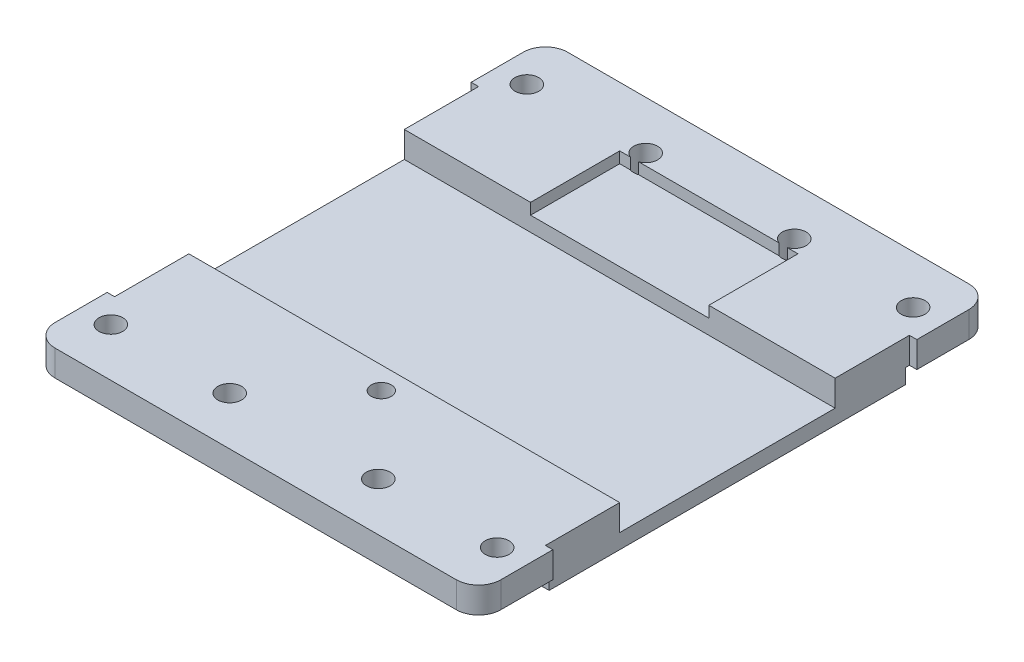
SolidWorks part; units mm, degrees
ref_plane "Front Plane" through (0, 0, 0) normal (0, 0, 1) x (1, 0, 0)
ref_plane "Top Plane" through (0, 0, 0) normal (0, 1, 0) x (1, 0, 0)
ref_plane "Right Plane" through (0, 0, 0) normal (1, 0, 0) x (0, 0, -1)
sketch "Sketch1" plane through (0, 0, 0) normal (0, 1, 0) x (1, 0, 0)
  line L0 (23.0945, -31.0966) -> (27.0945, -31.0966)
  line L1 (30.0945, -28.0966) -> (30.0945, -20.5966)
  line L2 (30.0945, -20.5966) -> (-29.9055, -20.5966)
  line L3 (-29.9055, -20.5966) -> (-29.9055, -28.0966)
  line L4 (-26.9055, -31.0966) -> (-24.9055, -31.0966)
  line L5 (-24.9055, -31.0966) -> (-24.9055, -29.0966)
  line L6 (-24.9055, -29.0966) -> (-14.9055, -29.0966)
  line L7 (-14.9055, -29.0966) -> (-14.9055, -31.0966)
  line L8 (-14.9055, -31.0966) -> (13.0945, -31.0966)
  line L9 (13.0945, -31.0966) -> (13.0945, -29.0966)
  line L10 (13.0945, -29.0966) -> (23.0945, -29.0966)
  line L11 (23.0945, -29.0966) -> (23.0945, -31.0966)
  line L12 (-22.9055, 37.9034) -> (-26.9055, 37.9034)
  line L13 (-29.9055, 34.9034) -> (-29.9055, 27.4034)
  line L14 (-29.9055, 27.4034) -> (30.0945, 27.4034)
  line L15 (30.0945, 27.4034) -> (30.0945, 34.9034)
  line L16 (27.0945, 37.9034) -> (25.0945, 37.9034)
  line L17 (25.0945, 37.9034) -> (25.0945, 35.9034)
  line L18 (25.0945, 35.9034) -> (15.0945, 35.9034)
  line L19 (15.0945, 35.9034) -> (15.0945, 37.9034)
  line L20 (15.0945, 37.9034) -> (-12.9055, 37.9034)
  line L21 (-12.9055, 37.9034) -> (-12.9055, 35.9034)
  line L22 (-12.9055, 35.9034) -> (-22.9055, 35.9034)
  line L23 (-22.9055, 35.9034) -> (-22.9055, 37.9034)
  line L24 (30.0945, 27.4034) -> (30.0945, -20.5966)
  line L25 (-29.9055, 27.4034) -> (-29.9055, -20.5966)
  arc A0 (27.0945, -31.0966) -> (30.0945, -28.0966) centre (27.0945, -28.0966) ccw
  arc A1 (-29.9055, -28.0966) -> (-26.9055, -31.0966) centre (-26.9055, -28.0966) ccw
  arc A2 (-26.9055, 37.9034) -> (-29.9055, 34.9034) centre (-26.9055, 34.9034) ccw
  arc A3 (30.0945, 34.9034) -> (27.0945, 37.9034) centre (27.0945, 34.9034) ccw
extrude "Boss-Extrude1" add sketch "Sketch1" along normal blind 2 contours L14 L25 L2 L24 | L3 A1 L4 L5 L6 L7 L8 L9 L10 L11 L0 A0 L1 L2 | L15 A3 L16 L17 L18 L19 L20 L21 L22 L23 L12 A2 L13 L14
sketch "Sketch2" plane through (0, 2, 0) normal (0, 1, 0) x (1, 0, 0)
  line L1 (-50.1539, 17.9034) -> (43.4526, 17.9034)
  line L2 (-50.1539, 17.9034) -> (-50.1539, -11.0966)
  line L3 (-50.1539, -11.0966) -> (43.4526, -11.0966)
  line L4 (43.4526, 17.9034) -> (43.4526, -11.0966)
  line L20 (30.0945, -28.0966) -> (30.0945, 34.9034)
  line L21 (27.0945, 37.9034) -> (25.0945, 37.9034)
  line L22 (25.0945, 37.9034) -> (25.0945, 35.9034)
  line L23 (25.0945, 35.9034) -> (15.0945, 35.9034)
  line L24 (15.0945, 35.9034) -> (15.0945, 37.9034)
  line L25 (15.0945, 37.9034) -> (-12.9055, 37.9034)
  line L26 (-12.9055, 37.9034) -> (-12.9055, 35.9034)
  line L27 (-12.9055, 35.9034) -> (-22.9055, 35.9034)
  line L28 (-22.9055, 35.9034) -> (-22.9055, 37.9034)
  line L29 (-22.9055, 37.9034) -> (-26.9055, 37.9034)
  line L30 (-29.9055, 34.9034) -> (-29.9055, -28.0966)
  line L31 (-26.9055, -31.0966) -> (-24.9055, -31.0966)
  line L32 (-24.9055, -31.0966) -> (-24.9055, -29.0966)
  line L33 (-24.9055, -29.0966) -> (-14.9055, -29.0966)
  line L34 (-14.9055, -29.0966) -> (-14.9055, -31.0966)
  line L35 (-14.9055, -31.0966) -> (13.0945, -31.0966)
  line L36 (13.0945, -31.0966) -> (13.0945, -29.0966)
  line L37 (13.0945, -29.0966) -> (23.0945, -29.0966)
  line L38 (23.0945, -29.0966) -> (23.0945, -31.0966)
  line L39 (23.0945, -31.0966) -> (27.0945, -31.0966)
  line L40 (30.0945, -28.0966) -> (30.0945, 34.9034)
  line L41 (27.0945, 37.9034) -> (25.0945, 37.9034)
  line L42 (25.0945, 37.9034) -> (25.0945, 35.9034)
  line L43 (25.0945, 35.9034) -> (15.0945, 35.9034)
  line L44 (15.0945, 35.9034) -> (15.0945, 37.9034)
  line L45 (15.0945, 37.9034) -> (-12.9055, 37.9034)
  line L46 (-12.9055, 37.9034) -> (-12.9055, 35.9034)
  line L47 (-12.9055, 35.9034) -> (-22.9055, 35.9034)
  line L48 (-22.9055, 35.9034) -> (-22.9055, 37.9034)
  line L49 (-22.9055, 37.9034) -> (-26.9055, 37.9034)
  line L50 (-29.9055, 34.9034) -> (-29.9055, -28.0966)
  line L51 (-26.9055, -31.0966) -> (-24.9055, -31.0966)
  line L52 (-24.9055, -31.0966) -> (-24.9055, -29.0966)
  line L53 (-24.9055, -29.0966) -> (-14.9055, -29.0966)
  line L54 (-14.9055, -29.0966) -> (-14.9055, -31.0966)
  line L55 (-14.9055, -31.0966) -> (13.0945, -31.0966)
  line L56 (13.0945, -31.0966) -> (13.0945, -29.0966)
  line L57 (13.0945, -29.0966) -> (23.0945, -29.0966)
  line L58 (23.0945, -29.0966) -> (23.0945, -31.0966)
  line L59 (23.0945, -31.0966) -> (27.0945, -31.0966)
  arc A4 (30.0945, 34.9034) -> (27.0945, 37.9034) centre (27.0945, 34.9034) ccw
  arc A5 (-26.9055, 37.9034) -> (-29.9055, 34.9034) centre (-26.9055, 34.9034) ccw
  arc A6 (-29.9055, -28.0966) -> (-26.9055, -31.0966) centre (-26.9055, -28.0966) ccw
  arc A7 (27.0945, -31.0966) -> (30.0945, -28.0966) centre (27.0945, -28.0966) ccw
  arc A8 (30.0945, 34.9034) -> (27.0945, 37.9034) centre (27.0945, 34.9034) ccw
  arc A9 (-26.9055, 37.9034) -> (-29.9055, 34.9034) centre (-26.9055, 34.9034) ccw
  arc A10 (-29.9055, -28.0966) -> (-26.9055, -31.0966) centre (-26.9055, -28.0966) ccw
  arc A11 (27.0945, -31.0966) -> (30.0945, -28.0966) centre (27.0945, -28.0966) ccw
  line M29 (30.0945, -28.0966) -> (30.0945, 34.9034)
  arc M30 (30.0945, 34.9034) -> (27.0945, 37.9034) centre (27.0945, 34.9034) ccw
  line M31 (27.0945, 37.9034) -> (25.0945, 37.9034)
  line M32 (25.0945, 37.9034) -> (25.0945, 35.9034)
  line M33 (25.0945, 35.9034) -> (15.0945, 35.9034)
  line M34 (15.0945, 35.9034) -> (15.0945, 37.9034)
  line M35 (15.0945, 37.9034) -> (-12.9055, 37.9034)
  line M36 (-12.9055, 37.9034) -> (-12.9055, 35.9034)
  line M37 (-12.9055, 35.9034) -> (-22.9055, 35.9034)
  line M38 (-22.9055, 35.9034) -> (-22.9055, 37.9034)
  line M39 (-22.9055, 37.9034) -> (-26.9055, 37.9034)
  arc M40 (-26.9055, 37.9034) -> (-29.9055, 34.9034) centre (-26.9055, 34.9034) ccw
  line M41 (-29.9055, 34.9034) -> (-29.9055, -28.0966)
  arc M42 (-29.9055, -28.0966) -> (-26.9055, -31.0966) centre (-26.9055, -28.0966) ccw
  line M43 (-26.9055, -31.0966) -> (-24.9055, -31.0966)
  line M44 (-24.9055, -31.0966) -> (-24.9055, -29.0966)
  line M45 (-24.9055, -29.0966) -> (-14.9055, -29.0966)
  line M46 (-14.9055, -29.0966) -> (-14.9055, -31.0966)
  line M47 (-14.9055, -31.0966) -> (13.0945, -31.0966)
  line M48 (13.0945, -31.0966) -> (13.0945, -29.0966)
  line M49 (13.0945, -29.0966) -> (23.0945, -29.0966)
  line M50 (23.0945, -29.0966) -> (23.0945, -31.0966)
  line M51 (23.0945, -31.0966) -> (27.0945, -31.0966)
  arc M52 (27.0945, -31.0966) -> (30.0945, -28.0966) centre (27.0945, -28.0966) ccw
  dimension "D2" = 20
  dimension "D3" = 20
  dimension "D1" = 0
extrude "Boss-Extrude2" add sketch "Sketch2" along normal blind 3.5 contours L3 M41 M42 M43 M44 M45 M46 M47 M48 M49 M50 M51 M52 M29 | L1 M41 M29 M30 M31 M32 M33 M34 M35 M36 M37 M38 M39 M40
sketch "Sketch3" plane through (0, 5.5, 0) normal (0, 1, 0) x (1, 0, 0)
  line L0 (-29.9055, 17.9034) -> (-29.9055, -11.0966) construction
  line L1 (-35.4293, 27.9034) -> (-28.9055, 27.9034)
  line L2 (-35.4293, 27.9034) -> (-35.4293, -21.0966)
  line L3 (-35.4293, -21.0966) -> (-28.9055, -21.0966)
  line L4 (-28.9055, 27.9034) -> (-28.9055, -21.0966)
  line L5 (-14.9055, -31.0966) -> (13.0945, -31.0966) construction
  line L6 (15.0945, 37.9034) -> (-12.9055, 37.9034) construction
  line L7 (0.0945, 47.5005) -> (0.0945, -43.4412)
  line L8 (30.0945, 17.9034) -> (30.0945, -11.0966) construction
  line L9 (35.6184, -21.0966) -> (29.0945, -21.0966)
  line L10 (29.0945, 27.9034) -> (29.0945, -21.0966)
  line L11 (35.6184, 27.9034) -> (29.0945, 27.9034)
  line L12 (35.6184, 27.9034) -> (35.6184, -21.0966)
  dimension "D1" = 1
  dimension "D2" = 10
  dimension "D3" = 10
  dimension "D4" = 30
extrude "Cut-Extrude2" cut sketch "Sketch3" against normal blind 15 contours L12 L9 L10 L11 | L2 L3 L4 L1
sketch "Sketch4" plane through (0, 5.5, 0) normal (0, 1, 0) x (1, 0, 0)
  line L0 (-28.9055, 17.9034) -> (29.0945, 17.9034) construction
  line L1 (12.0945, 17.9034) -> (-11.9055, 17.9034)
  line L2 (12.0945, 17.9034) -> (12.0945, 29.9034)
  line L3 (12.0945, 29.9034) -> (-11.9055, 29.9034)
  line L4 (-11.9055, 17.9034) -> (-11.9055, 29.9034)
  line L5 (-28.9055, 27.9034) -> (-28.9055, 17.9034) construction
  dimension "D1" = 24
  dimension "D2" = 17
  dimension "D3" = 12
extrude "Cut-Extrude3" cut sketch "Sketch4" against normal blind 1.5
sketch "Sketch5" plane through (0, 5.5, 0) normal (0, 1, 0) x (1, 0, 0)
  line L0 (-28.9055, -11.0966) -> (29.0945, -11.0966) construction
  circle A0 centre (0, -14.0966) radius 1.35
  dimension "D1" = 2.7
  dimension "D2" = 3
extrude "Cut-Extrude4" cut sketch "Sketch5" against normal blind 3
sketch "Sketch6" plane through (0, 5.5, 0) normal (0, 1, 0) x (1, 0, 0)
  line L0 (-28.9055, -11.0966) -> (29.0945, -11.0966) construction
  line L1 (-28.9055, -11.0966) -> (29.0945, -11.0966) construction
  line L2 (52.5689, 3.4034) -> (-47.2679, 3.4034)
  line L3 (26.0945, 40.4034) -> (-25.9055, 40.4034) construction
  circle A0 centre (-20.188, -19.0966) radius 1.35
  circle A1 centre (0, -25.0966) radius 1.35
  circle A2 centre (20.7703, -19.0966) radius 1.35
  circle A3 centre (-20.188, 25.9034) radius 1.35
  circle A4 centre (0, 31.9034) radius 1.35
  circle A5 centre (20.7703, 25.9034) radius 1.35
  dimension "D1" = 8
  dimension "D2" = 14
  dimension "D3" = 8
  dimension "D4" = 2.7
  dimension "D5" = 2.7
  dimension "D6" = 2.7
  dimension "D7" = 37
extrude "Cut-Extrude5" cut sketch "Sketch6" against normal blind 3 contours A5 | A4 | A3 | A0 | A1 | A2
sketch "Sketch7" plane through (0, 0, 0) normal (0, -1, 0) x (1, 0, 0)
  line L0 (15.0945, -37.9034) -> (-12.9055, -37.9034) construction
  line L1 (-33.8076, 32.9113) -> (36.1224, 32.9113)
  line L2 (-33.8076, 32.9113) -> (-33.8076, 20.5966)
  line L3 (-33.8076, 20.5966) -> (36.1224, 20.5966)
  line L4 (36.1224, 32.9113) -> (36.1224, 20.5966)
  line L5 (-36.6663, -27.4034) -> (40.7404, -27.4034)
  line L6 (-36.6663, -27.4034) -> (-36.6663, -43.6031)
  line L7 (-36.6663, -43.6031) -> (40.7404, -43.6031)
  line L8 (40.7404, -27.4034) -> (40.7404, -43.6031)
  line L9 (-14.9055, 31.0966) -> (13.0945, 31.0966) construction
  dimension "D1" = 10.5
  dimension "D2" = 10.5
extrude "Cut-Extrude6" cut sketch "Sketch7" against normal blind 2
sketch "Sketch8" plane through (0, 2, 0) normal (0, -1, 0) x (1, 0, 0)
  line L0 (13.0945, 31.0966) -> (-14.9055, 31.0966) construction
  line L1 (30.0945, 28.0966) -> (30.0945, 21.0966) construction
  line L2 (-56.3939, -3.4034) -> (64.5651, -3.4034)
  line L3 (-12.9055, -37.9034) -> (15.0945, -37.9034) construction
  line L4 (0.0945, 49.059) -> (0.0945, -54.2227)
  circle A2 centre (10.0945, 24.5966) radius 1.6
  circle A3 centre (26.0945, 24.5966) radius 1.6
  circle A4 centre (-25.9055, 24.5966) radius 1.6
  circle A5 centre (-9.9055, 24.5966) radius 1.6
  circle A6 centre (26.0945, -31.4034) radius 1.6
  circle A7 centre (10.0945, -31.4034) radius 1.6
  circle A8 centre (-9.9055, -31.4034) radius 1.6
  circle A9 centre (-25.9055, -31.4034) radius 1.6
  dimension "D1" = 6.5
  dimension "D2" = 3.2
  dimension "D4" = 4
  dimension "D5" = 3.2
  dimension "D6" = 20
  dimension "D3" = 6.5
  dimension "D7" = 34.5
  dimension "D8" = 30
extrude "Cut-Extrude7" cut sketch "Sketch8" against normal blind 18 contours A9 | A8 | A7 | A6 | A3 | A2 | A5 | A4
sketch "Sketch9" plane through (0, 5.5, 0) normal (0, 1, 0) x (1, 0, 0)
  line L0 (12.0945, 29.9034) -> (10.6513, 29.9034) construction
  line L1 (-3.7538, -21.8858) -> (2.8434, -21.8858)
  line L2 (-3.7538, -21.8858) -> (-3.7538, -28.1897)
  line L3 (-3.7538, -28.1897) -> (2.8434, -28.1897)
  line L4 (2.8434, -21.8858) -> (2.8434, -28.1897)
  line L5 (17.4304, -16.3881) -> (23.3679, -16.3881)
  line L6 (17.4304, -16.3881) -> (17.4304, -21.8858)
  line L7 (17.4304, -21.8858) -> (23.3679, -21.8858)
  line L8 (23.3679, -16.3881) -> (23.3679, -21.8858)
  line L9 (-25.1579, -16.3881) -> (-17.388, -16.3881)
  line L10 (-25.1579, -16.3881) -> (-25.1579, -21.8858)
  line L11 (-25.1579, -21.8858) -> (-17.388, -21.8858)
  line L12 (-17.388, -16.3881) -> (-17.388, -21.8858)
  line L13 (-23.3254, 28.8391) -> (-18.1943, 28.8391)
  line L14 (-23.3254, 28.8391) -> (-23.3254, 23.6347)
  line L15 (-23.3254, 23.6347) -> (-18.1943, 23.6347)
  line L16 (-18.1943, 28.8391) -> (-18.1943, 23.6347)
  line L17 (-2.6543, 34.9965) -> (2.8434, 34.9965)
  line L18 (-2.6543, 34.9965) -> (-2.6543, 29.9034)
  line L19 (-2.6543, 29.9034) -> (2.8434, 29.9034)
  line L20 (2.8434, 34.9965) -> (2.8434, 29.9034)
  line L22 (18.0168, 28.8391) -> (22.7082, 28.8391)
  line L23 (18.0168, 28.8391) -> (18.0168, 23.6347)
  line L24 (18.0168, 23.6347) -> (22.7082, 23.6347)
  line L25 (22.7082, 28.8391) -> (22.7082, 23.6347)
extrude "Boss-Extrude3" add sketch "Sketch9" against normal up to surface (3.5 mm away) up to face at (-9.9055, 2, 22.9966)
sketch "Sketch10" plane through (0, 2, 0) normal (0, -1, 0) x (1, 0, 0)
  line L1 (-24.9055, 31.0966) -> (-11.2318, 31.0966)
  line L2 (-24.9055, 31.0966) -> (-24.9055, 28.4099)
  line L3 (-24.9055, 28.4099) -> (-11.2318, 28.4099)
  line L4 (-11.2318, 31.0966) -> (-11.2318, 28.4099)
  line L5 (13.0945, 31.0966) -> (24.0062, 31.0966)
  line L6 (13.0945, 31.0966) -> (13.0945, 27.9556)
  line L7 (13.0945, 27.9556) -> (24.0062, 27.9556)
  line L8 (24.0062, 31.0966) -> (24.0062, 27.9556)
  line L9 (-23.8272, -34.849) -> (-12.9055, -34.849)
  line L10 (-23.8272, -34.849) -> (-23.8272, -37.9034)
  line L11 (-23.8272, -37.9034) -> (-12.9055, -37.9034)
  line L12 (-12.9055, -34.849) -> (-12.9055, -37.9034)
  line L13 (13.0945, -34.849) -> (25.0945, -34.849)
  line L14 (13.0945, -34.849) -> (13.0945, -37.9034)
  line L15 (13.0945, -37.9034) -> (25.0945, -37.9034)
  line L16 (25.0945, -34.849) -> (25.0945, -37.9034)
extrude "Boss-Extrude4" add sketch "Sketch10" against normal up to vertex (3.5 mm away)
